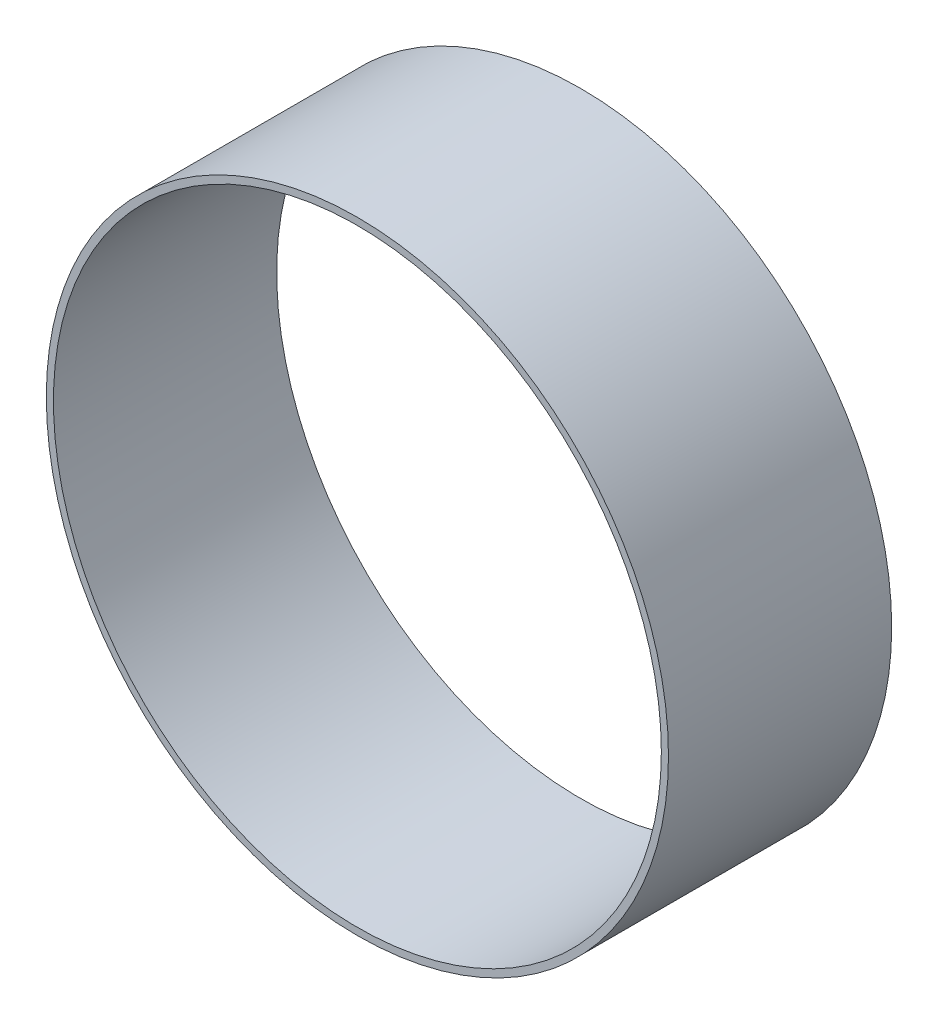
SolidWorks part; units mm, degrees
ref_plane "Front" through (0, 0, 0) normal (0, 0, 1) x (1, 0, 0)
ref_plane "Top" through (0, 0, 0) normal (0, 1, 0) x (1, 0, 0)
ref_plane "Right" through (0, 0, 0) normal (1, 0, 0) x (0, 0, -1)
sketch "Sketch1" plane through (0, 0, 0) normal (0, 0, 1) x (1, 0, 0)
  circle A0 centre (0, 0) radius 203.2
  circle A1 centre (0, 0) radius 207.9625
  dimension "D1" = 406.4
  dimension "D2" = 415.925
extrude "Boss-Extrude1" add sketch "Sketch1" along normal mid plane 149.225
